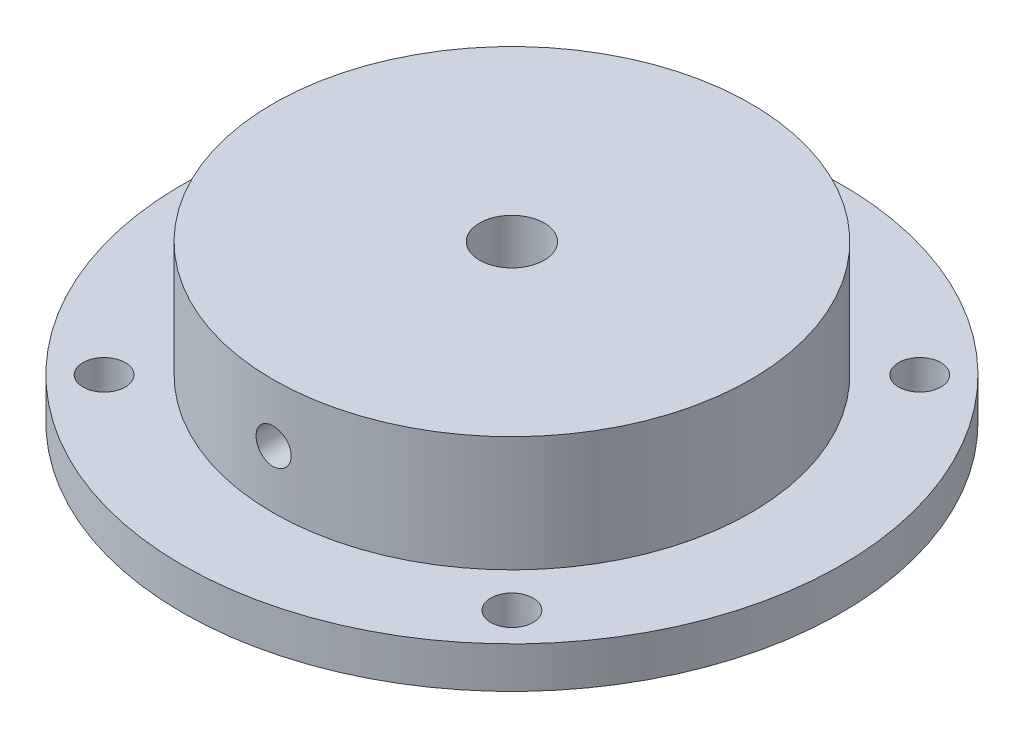
SolidWorks part; units mm, degrees
material "6061-T6 (SS)"
ref_plane "Front Plane" through (0, 0, 0) normal (0, 0, 1) x (1, 0, 0)
ref_plane "Top Plane" through (0, 0, 0) normal (0, 1, 0) x (1, 0, 0)
ref_plane "Right Plane" through (0, 0, 0) normal (1, 0, 0) x (0, 0, -1)
sketch "Sketch10" plane through (0, 0, 0) normal (0, 1, 0) x (1, 0, 0)
  line L0 (-15.7154, 15.7154) -> (-15.7154, -15.7154) construction
  line L1 (-15.7154, 15.7154) -> (15.7154, 15.7154) construction
  line L2 (15.7154, -15.7154) -> (15.7154, 15.7154) construction
  line L3 (15.7154, -15.7154) -> (-15.7154, -15.7154) construction
  circle A5 centre (0, 0) radius 25.4
  point P11 (15.7154, 15.7154)
  point P12 (-15.7154, 15.7154)
  point P14 (-15.7154, -15.7154)
  point P15 (15.7154, -15.7154)
  dimension "D10" = 50.8
  dimension "D2" = 22.225
  dimension "D3" = 22.225
  dimension "D4" = 22.225
extrude "Boss-Extrude1" add sketch "Sketch10" along normal blind 3.175
sketch "Sketch13" plane through (0, 3.175, 0) normal (0, 1, 0) x (1, 0, 0)
  circle A0 centre (0, 0) radius 18.415
  dimension "D1" = 36.83
extrude "Boss-Extrude2" add sketch "Sketch13" along normal blind 8.89
hole_wizard "#9 (0.196) Diameter Hole1" positions "Sketch15" profile "Sketch14" hole size "#9" standard "ANSI Inch" end condition through all
sketch "Sketch15" plane through (0, 12.065, 0) normal (0, 1, 0) x (1, 0, 0)
  point P0 (0, 0)
sketch "Sketch14" plane through (0, 12.065, 0) normal (1, 0, 0) x (0, 0, 1)
  line L0 (0, 0) -> (0, 12.065)
  line L1 (0, 12.065) -> (2.4892, 12.065)
  line L2 (2.4892, 12.065) -> (2.4892, 0)
  line L5 (2.4892, 0) -> (0, 0)
  line L11 (0, -6.35) -> (0, 107.95) construction
  dimension "Thru Hole Dia." = 4.9784
  dimension "Thru Hole Depth" = 12.065
hole_wizard "#6-32 Tapped Hole2" positions "Sketch19" profile "Sketch18" tap size "#6-32" standard "ANSI Inch"
sketch "Sketch19" plane through (0, 0, 0) normal (0, 0, 1) x (1, 0, 0)
  point P0 (0, 7.62)
  dimension "D1" = 7.62
sketch "Sketch18" plane through (0, 7.62, 0) normal (1, 0, 0) x (0, 1, 0)
  line L0 (0, 0) -> (0, 25.4)
  line L1 (0, 25.4) -> (1.3525, 25.4)
  line L2 (1.3525, 25.4) -> (1.3525, 0)
  line L5 (1.3525, 0) -> (0, 0)
  line L11 (0, -6.35) -> (0, 107.95) construction
  dimension "Thread Major Dia." = 2.7051
  dimension "Thru Tap Drill Depth" = 25.4
hole_wizard "#4 Clearance Hole2" positions "Sketch23" profile "Sketch22" hole size "#4" standard "ANSI Inch"
sketch "Sketch23" plane through (0, 0, 0) normal (0, -1, 0) x (-1, 0, 0)
  point P0 (-15.7154, -15.7154)
  point P3 (15.7154, -15.7154)
  point P6 (15.7154, 15.7154)
  point P9 (-15.7154, 15.7154)
sketch "Sketch22" plane through (15.7154, 0, 15.7154) normal (1, 0, 0) x (0, 0, -1)
  line L0 (0, 0) -> (0, 4.2826)
  line L1 (0, 4.2826) -> (1.6319, 3.302)
  line L2 (1.6319, 3.302) -> (1.6319, 0)
  line L5 (1.6319, 0) -> (0, 0)
  line L10 (0, 4.2826) -> (-1.6319, 3.302) construction
  line L11 (0, -6.35) -> (0, 107.95) construction
  dimension "Hole Dia." = 3.2639
  dimension "Hole Depth" = 3.302
  dimension "Drill Angle" = 118
